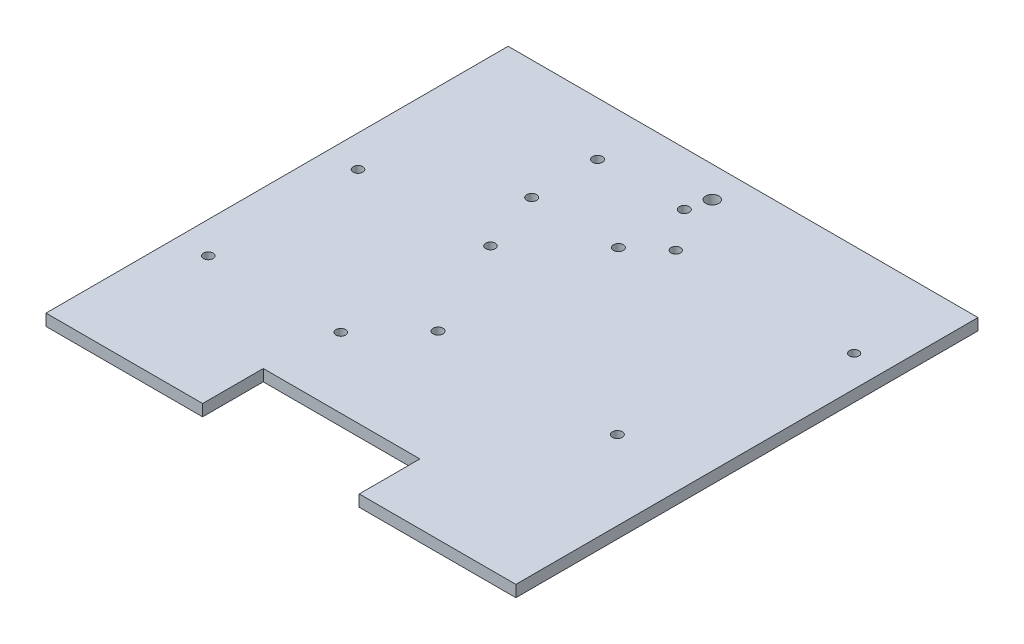
SolidWorks part; units mm, degrees
ref_plane "Front Plane" through (0, 0, 0) normal (0, 0, 1) x (1, 0, 0)
ref_plane "Top Plane" through (0, 0, 0) normal (0, 1, 0) x (1, 0, 0)
ref_plane "Right Plane" through (0, 0, 0) normal (1, 0, 0) x (0, 0, -1)
sketch "Sketch1" plane through (0, 0, 0) normal (0, 1, 0) x (1, 0, 0)
  line L1 (-96.84, -95.25) -> (96.84, -95.25)
  line L2 (-96.84, -95.25) -> (-96.84, 95.25)
  line L3 (-96.84, 95.25) -> (96.84, 95.25)
  line L4 (96.84, -95.25) -> (96.84, 95.25)
  line L5 (-96.84, -95.25) -> (96.84, 95.25) construction
  line L6 (-96.84, 95.25) -> (96.84, -95.25) construction
  point P0 (0, 0)
  dimension "D1" = 193.68
  dimension "D2" = 190.5
extrude "Boss-Extrude1" add sketch "Sketch1" along normal blind 4.78
sketch "Sketch2" plane through (0, 4.78, 0) normal (0, 1, 0) x (1, 0, 0)
  line L0 (96.84, 95.25) -> (-96.84, 95.25) construction
  line L1 (96.84, -95.25) -> (96.84, 95.25) construction
  circle A0 centre (0, 82.55) radius 2.6797
  point P4 (0, 95.25)
  dimension "D1" = 5.3594
  dimension "D2" = 12.7
  dimension "D3" = 96.84
extrude "Cut-Extrude1" cut sketch "Sketch2" against normal through all
sketch "Sketch3" plane through (0, 4.78, 0) normal (0, 1, 0) x (1, 0, 0)
  line L0 (0, -95.25) -> (-32.28, -95.25)
  line L1 (-96.84, -95.25) -> (96.84, -95.25) construction
  line L2 (-32.28, -95.25) -> (-32.28, -70.25)
  line L3 (-32.28, -70.25) -> (32.28, -70.25)
  line L4 (32.28, -70.25) -> (32.28, -95.25)
  line L5 (32.28, -95.25) -> (0, -95.25)
  line L6 (96.84, -95.25) -> (96.84, 95.25) construction
  dimension "D1" = 64.56
  dimension "D2" = 64.56
  dimension "D3" = 25
extrude "Cut-Extrude2" cut sketch "Sketch3" against normal through all
sketch "Sketch4" plane through (0, 4.78, 0) normal (0, 1, 0) x (1, 0, 0)
  line L7 (-40.88, 76.2) -> (0.3, 76.2)
  line L8 (-40.88, 76.2) -> (-40.88, 43.2)
  line L9 (-40.88, 43.2) -> (0.3, 43.2)
  line L10 (0.3, 76.2) -> (0.3, 43.2)
  line L11 (-40.88, 76.2) -> (0.3, 43.2) construction
  line L12 (-40.88, 43.2) -> (0.3, 76.2) construction
  line L13 (6.65, 82.55) -> (87.95, 82.55)
  line L14 (6.65, 82.55) -> (6.65, 31.53)
  line L15 (6.65, 31.53) -> (87.95, 31.53)
  line L16 (87.95, 82.55) -> (87.95, 31.53)
  line L17 (6.65, 82.55) -> (87.95, 31.53) construction
  line L18 (6.65, 31.53) -> (87.95, 82.55) construction
  line L19 (-40.88, 59.7) -> (0.3, 59.7) construction
  line L20 (-87.95, -57.892) -> (-87.95, 36.85)
  line L21 (-87.95, 36.85) -> (-25.085, 36.85)
  line L22 (-25.085, 36.85) -> (-25.085, -57.892)
  line L23 (-25.085, -57.892) -> (-87.95, -57.892)
  line L24 (96.84, 95.25) -> (-96.84, 95.25) construction
  line L25 (-96.84, 95.25) -> (-96.84, -95.25) construction
  line L26 (96.84, -95.25) -> (96.84, 95.25) construction
  line L28 (-12.385, -63.9) -> (66.745, -63.9)
  line L29 (-12.385, -63.9) -> (-12.385, 8.1)
  line L30 (-12.385, 8.1) -> (66.745, 8.1)
  line L31 (66.745, -63.9) -> (66.745, 8.1)
  line L32 (-12.385, -63.9) -> (66.745, 8.1) construction
  line L33 (-12.385, 8.1) -> (66.745, -63.9) construction
  line L34 (32.28, -70.25) -> (-32.28, -70.25) construction
  circle A2 centre (10.5225, 56.9625) radius 1.9362
  circle A3 centre (84.0775, 56.9625) radius 1.9362
  circle A4 centre (-38.005, 73.275) radius 2.0487
  circle A5 centre (-2.255, 73.275) radius 2.0487
  circle A6 centre (-2.255, 46.125) radius 2.0487
  circle A7 centre (-38.005, 46.125) radius 2.0487
  circle A8 centre (-83.8225, -41.382) radius 1.9812
  circle A9 centre (-83.8225, 20.34) radius 1.9812
  circle A10 centre (-29.2125, 20.34) radius 1.9812
  circle A11 centre (-29.2125, -41.382) radius 1.9812
  circle A14 centre (64.27, -20.865) radius 2.0387
  circle A15 centre (-9.61, -20.865) radius 2.0387
  circle A16 centre (0, 82.55) radius 2.6797 construction
  point P0 (27.18, -27.9)
  point P11 (-20.29, 59.7)
  point P16 (47.3, 57.04)
  dimension "D4" = 79.13
  dimension "D5" = 72
  dimension "D6" = 73.88
  dimension "D7" = 4.0774
  dimension "D13" = 3.8724
  dimension "D15" = 3.8724
  dimension "D20" = 4.0974
  dimension "D24" = 3.9624
  dimension "D30" = 54.61
  dimension "D31" = 61.722
  dimension "D32" = 54.61
  dimension "D33" = 6.35
  dimension "D8" = 41.18
  dimension "D9" = 33
  dimension "D10" = 81.3
  dimension "D11" = 51.02
  dimension "D12" = 12.7
  dimension "D14" = 25.4325
  dimension "D16" = 25.4325
  dimension "D17" = 3.8725
  dimension "D18" = 3.8725
  dimension "D19" = 35.75
  dimension "D21" = 2.925
  dimension "D22" = 2.555
  dimension "D23" = 16.5
  dimension "D25" = 16.51
  dimension "D26" = 4.1275
  dimension "D27" = 62.865
  dimension "D28" = 94.742
  dimension "D29" = 19.05
  dimension "D34" = 8.89
  dimension "D35" = 8.89
  dimension "D36" = 6.35
  dimension "D37" = 2.775
  dimension "D38" = 43.035
  dimension "D39" = 6.35
  dimension "D40" = 12.7
extrude "Cut-Extrude3" cut sketch "Sketch4" against normal through all contours A14 | A15 | A3 | A2 | A5 | A4 | A7 | A6 | A9 | A10 | A11 | A8
